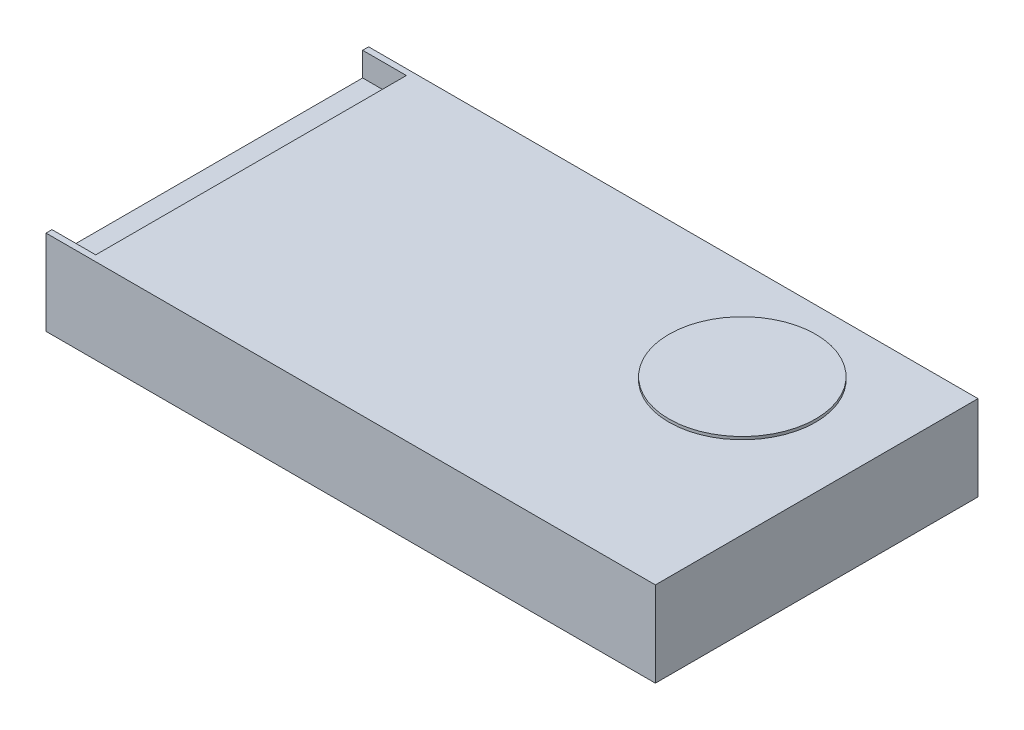
SolidWorks part; units mm, degrees
ref_plane "Front Plane" through (0, 0, 0) normal (0, 0, 1) x (1, 0, 0)
ref_plane "Top Plane" through (0, 0, 0) normal (0, 1, 0) x (1, 0, 0)
ref_plane "Right Plane" through (0, 0, 0) normal (1, 0, 0) x (0, 0, -1)
sketch "Sketch1" plane through (0, 0, 0) normal (0, 1, 0) x (1, 0, 0)
  line L1 (0, 0) -> (215.9, 0)
  line L2 (0, 0) -> (0, 114.3)
  line L3 (0, 114.3) -> (215.9, 114.3)
  line L4 (215.9, 0) -> (215.9, 114.3)
  dimension "D1" = 215.9
  dimension "D2" = 114.3
extrude "Boss-Extrude1" add sketch "Sketch1" along normal blind 30.17
sketch "Sketch2" plane through (0, 30.17, 0) normal (0, 1, 0) x (1, 0, 0)
  line L0 (0, 114.3) -> (0, 0) construction
  line L1 (0, 112.18) -> (15.5, 112.18)
  line L2 (0, 112.18) -> (0, 2.12)
  line L3 (0, 2.12) -> (15.5, 2.12)
  line L4 (15.5, 112.18) -> (15.5, 2.12)
  line L5 (215.9, 114.3) -> (0, 114.3) construction
  line L6 (0, 0) -> (215.9, 0) construction
  dimension "D1" = 15.5
  dimension "D2" = 2.12
  dimension "D3" = 2.12
extrude "Cut-Extrude1" cut sketch "Sketch2" against normal blind 8.5
sketch "Sketch3" plane through (0, 30.17, 0) normal (0, 1, 0) x (1, 0, 0)
  line L0 (215.9, 0) -> (215.9, 114.3) construction
  line L1 (215.9, 114.3) -> (0, 114.3) construction
  circle A0 centre (168.4, 78.3) radius 26
  dimension "D1" = 52
  dimension "D2" = 47.5
  dimension "D3" = 36
extrude "Boss-Extrude2" add sketch "Sketch3" along normal blind 1
